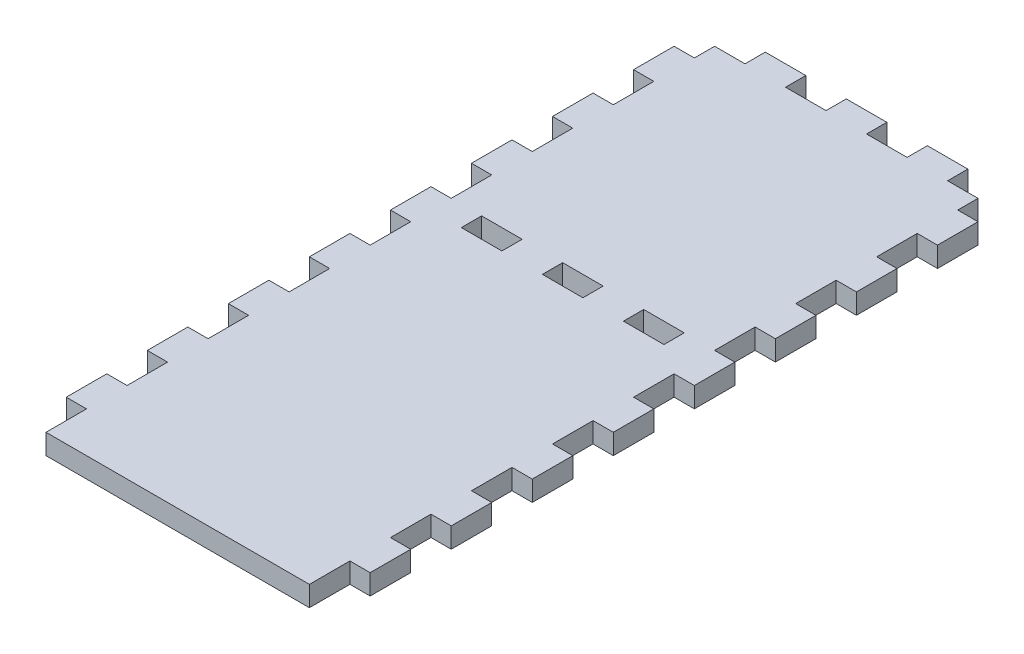
SolidWorks part; units mm, degrees
material "Pine"
ref_plane "Front Plane" through (0, 0, 0) normal (0, 0, 1) x (1, 0, 0)
ref_plane "Top Plane" through (0, 0, 0) normal (0, 1, 0) x (1, 0, 0)
ref_plane "Right Plane" through (0, 0, 0) normal (1, 0, 0) x (0, 0, -1)
sketch "Sketch1" plane through (0, 0, 0) normal (0, 1, 0) x (1, 0, 0)
  line L1 (0, 0) -> (95.25, 0)
  line L2 (0, 0) -> (0, 215.9)
  line L3 (0, 215.9) -> (95.25, 215.9)
  line L4 (95.25, 0) -> (95.25, 215.9)
  dimension "D1" = 95.25
  dimension "D2" = 215.9
extrude "Boss-Extrude1" add sketch "Sketch1" along normal blind 6.35
sketch "Sketch2" plane through (0, 6.35, 0) normal (0, 1, 0) x (1, 0, 0)
  line L0 (0, 215.9) -> (0, 0) construction
  line L1 (0, 203.2) -> (6.35, 203.2)
  line L2 (0, 203.2) -> (0, 215.9)
  line L3 (0, 215.9) -> (6.35, 215.9)
  line L4 (6.35, 203.2) -> (6.35, 215.9)
  line L5 (95.25, 215.9) -> (0, 215.9) construction
  line L6 (95.25, 0) -> (95.25, 215.9) construction
  line L7 (88.9, 215.9) -> (95.25, 215.9)
  line L8 (88.9, 215.9) -> (88.9, 203.2)
  line L9 (88.9, 203.2) -> (95.25, 203.2)
  line L10 (95.25, 215.9) -> (95.25, 203.2)
  dimension "D1" = 6.35
  dimension "D2" = 12.7
extrude "Cut-Extrude1" cut sketch "Sketch2" against normal through all
pattern_linear "LPattern1" count 10 spacing 25.4 along (0, 0, 1) of "Cut-Extrude1"
sketch "Sketch3" plane through (0, 6.35, 0) normal (0, 1, 0) x (1, 0, 0)
  line L0 (88.9, 215.9) -> (6.35, 215.9) construction
  line L1 (28.575, 215.9) -> (41.275, 215.9)
  line L2 (28.575, 215.9) -> (28.575, 209.55)
  line L3 (28.575, 209.55) -> (41.275, 209.55)
  line L4 (41.275, 215.9) -> (41.275, 209.55)
  point P6 (47.625, 215.9)
  dimension "D1" = 6.35
  dimension "D2" = 6.35
  dimension "D3" = 12.7
extrude "Cut-Extrude2" cut sketch "Sketch3" against normal through all
pattern_linear "LPattern2" count 2 spacing 25.4 along (-1, 0, 0) count 3 spacing 25.4 along (1, 0, 0) of "Cut-Extrude2"
sketch "Sketch4" plane through (0, 6.35, 0) normal (0, 1, 0) x (1, 0, 0)
  line L0 (0, 127) -> (6.35, 127) construction
  line L1 (15.875, 127) -> (28.575, 127)
  line L2 (15.875, 127) -> (15.875, 120.65)
  line L3 (15.875, 120.65) -> (28.575, 120.65)
  line L4 (28.575, 127) -> (28.575, 120.65)
  line L5 (41.275, 127) -> (53.975, 127)
  line L6 (41.275, 127) -> (41.275, 120.65)
  line L7 (41.275, 120.65) -> (53.975, 120.65)
  line L8 (53.975, 127) -> (53.975, 120.65)
  line L9 (66.675, 127) -> (79.375, 127)
  line L10 (66.675, 127) -> (66.675, 120.65)
  line L11 (66.675, 120.65) -> (79.375, 120.65)
  line L12 (79.375, 127) -> (79.375, 120.65)
  line L13 (15.875, 209.55) -> (15.875, 215.9) construction
  line L14 (41.275, 209.55) -> (41.275, 215.9) construction
  line L15 (66.675, 209.55) -> (66.675, 215.9) construction
  line L16 (28.575, 215.9) -> (28.575, 209.55) construction
extrude "Cut-Extrude3" cut sketch "Sketch4" against normal through all
